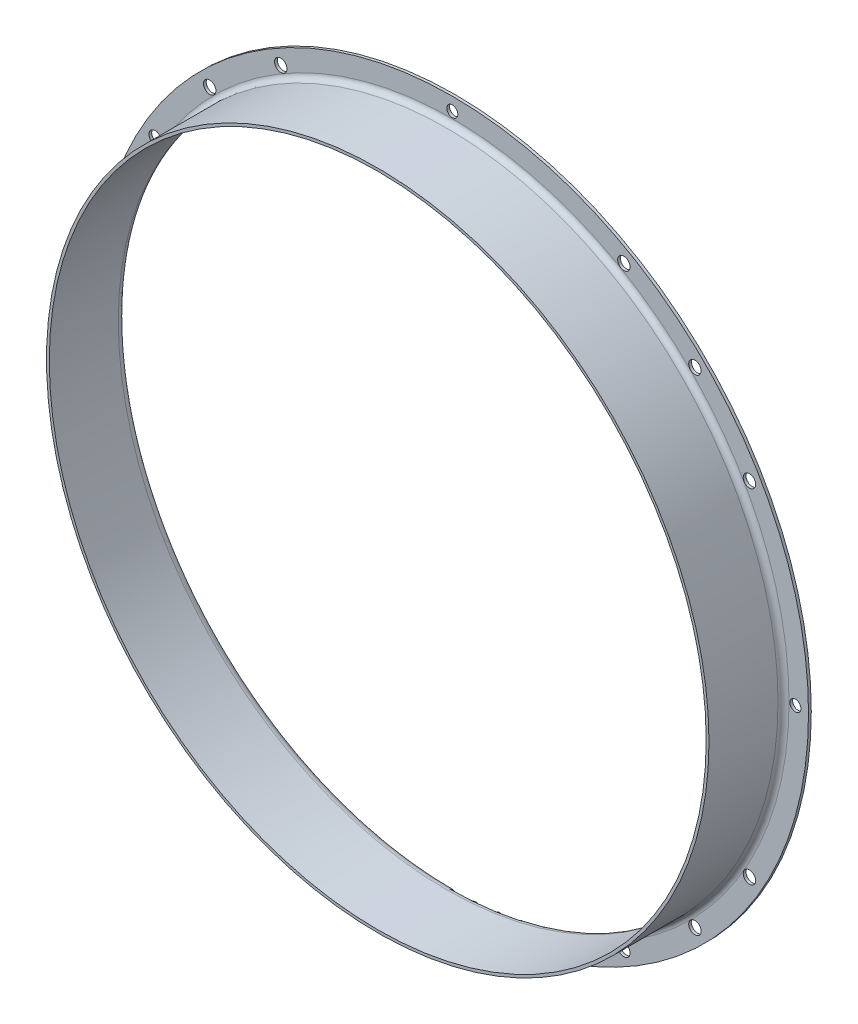
SolidWorks part; units mm, degrees
material "Thornel VCB-20 Carbon Cloth"
ref_plane "Front" through (0, 0, 0) normal (0, 0, 1) x (1, 0, 0)
ref_plane "Top" through (0, 0, 0) normal (0, 1, 0) x (1, 0, 0)
ref_plane "Right" through (0, 0, 0) normal (1, 0, 0) x (0, 0, -1)
sketch "Sketch1" plane through (0, 0, 0) normal (1, 0, 0) x (0, 0, -1)
  line L0 (-36.2891, 0) -> (0, 0) construction
  line L1 (0, 0) -> (0, 63.184) construction
  line L2 (0, 129) -> (0, 121.95)
  line L3 (-3, 118.95) -> (-28, 118.95)
  line L4 (-28, 118.95) -> (-28, 119.95)
  line L5 (-28, 119.95) -> (-3, 119.95)
  line L6 (-1, 121.95) -> (-1, 129)
  line L7 (-1, 129) -> (0, 129)
  arc A0 (0, 121.95) -> (-3, 118.95) centre (-3, 121.95) cw
  arc A1 (-1, 121.95) -> (-3, 119.95) centre (-3, 121.95) cw
  point P12 (0, 118.95)
  dimension "D1" = 3
  dimension "D2" = 2
  dimension "D3" = 1
  dimension "D4" = 1
  dimension "D5" = 129
  dimension "D6" = 28
  dimension "D7" = 237.9
revolve "Revolve1" add sketch "Sketch1" angle 360 about L0
hole_wizard "Ø4.5 (4.5) Diameter Hole1" positions "Sketch3" profile "Sketch4" hole size "Ø4.5" standard "Ansi Metric" end condition through all
sketch "Sketch3" plane through (0, 0, 1) normal (0, 0, 1) x (1, 0, 0)
  line L0 (62.125, 107.6037) -> (0, 0)
  line L2 (0, 65.193) -> (0, 26.1991) construction
  point P0 (62.125, 107.6037)
  dimension "D1" = 124.25
  dimension "D2" = 30
sketch "Sketch4" plane through (62.125, 107.6037, 1) normal (1, 0, 0) x (0, -1, 0)
  line L0 (0, 0) -> (0, 1)
  line L1 (0, 1) -> (2.25, 1)
  line L2 (2.25, 1) -> (2.25, 0)
  line L5 (2.25, 0) -> (0, 0)
  line L11 (0, -6.35) -> (0, 107.95) construction
  dimension "Thru Hole Dia." = 4.5
  dimension "Thru Hole Depth" = 1
ref_axis "Axis1" through (0, 0, -80.9) along (0, 0, 1)
pattern_circular "CirPattern1" count 12 over 360 about axis through (0, 0, -80.9) along (0, 0, 1) skipping 1, 4, 7, 10 of "Ø4.5 (4.5) Diameter Hole1"
hole_wizard "Ø4.0 (4) Diameter Hole1" positions "Sketch6" profile "Sketch5" hole size "Ø4.0" standard "Ansi Metric" end condition through all
sketch "Sketch6" plane through (0, 0, 1) normal (0, 0, 1) x (1, 0, 0)
  line L0 (107.6037, 62.125) -> (0, 0)
  line L2 (0, 0) -> (124.25, 0)
  point P1 (124.25, 0)
sketch "Sketch5" plane through (124.25, 0, 1) normal (1, 0, 0) x (0, -1, 0)
  line L0 (0, 0) -> (0, 1)
  line L1 (0, 1) -> (2, 1)
  line L2 (2, 1) -> (2, 0)
  line L5 (2, 0) -> (0, 0)
  line L11 (0, -6.35) -> (0, 107.95) construction
  dimension "Thru Hole Dia." = 4
  dimension "Thru Hole Depth" = 1
pattern_circular "CirPattern2" count 4 over 360 about axis through (0, 0, 0) along (0, 0, 1) of "Ø4.0 (4) Diameter Hole1"
hole_wizard "Ø4.5 (4.5) Diameter Hole2" positions "Sketch8" profile "Sketch7" hole size "Ø4.5" standard "Ansi Metric"
sketch "Sketch8" plane through (0, 0, 1) normal (0, 0, 1) x (1, 0, 0)
  line L0 (87.858, 87.858) -> (0, 0)
  line L1 (0, 0) -> (0, 124.25)
  point P0 (87.858, 87.858)
  dimension "D1" = 45
sketch "Sketch7" plane through (87.858, 87.858, 1) normal (1, 0, 0) x (0, -1, 0)
  line L0 (0, 0) -> (0, 2.8519)
  line L1 (0, 2.8519) -> (2.25, 1.5)
  line L2 (2.25, 1.5) -> (2.25, 0)
  line L5 (2.25, 0) -> (0, 0)
  line L10 (0, 2.8519) -> (-2.25, 1.5) construction
  line L11 (0, -6.35) -> (0, 107.95) construction
  dimension "Hole Dia." = 4.5
  dimension "Hole Depth" = 1.5
  dimension "Drill Angle" = 118
pattern_circular "CirPattern3" count 4 over 360 about axis through (0, 0, 0) along (0, 0, 1) of "Ø4.5 (4.5) Diameter Hole2"
